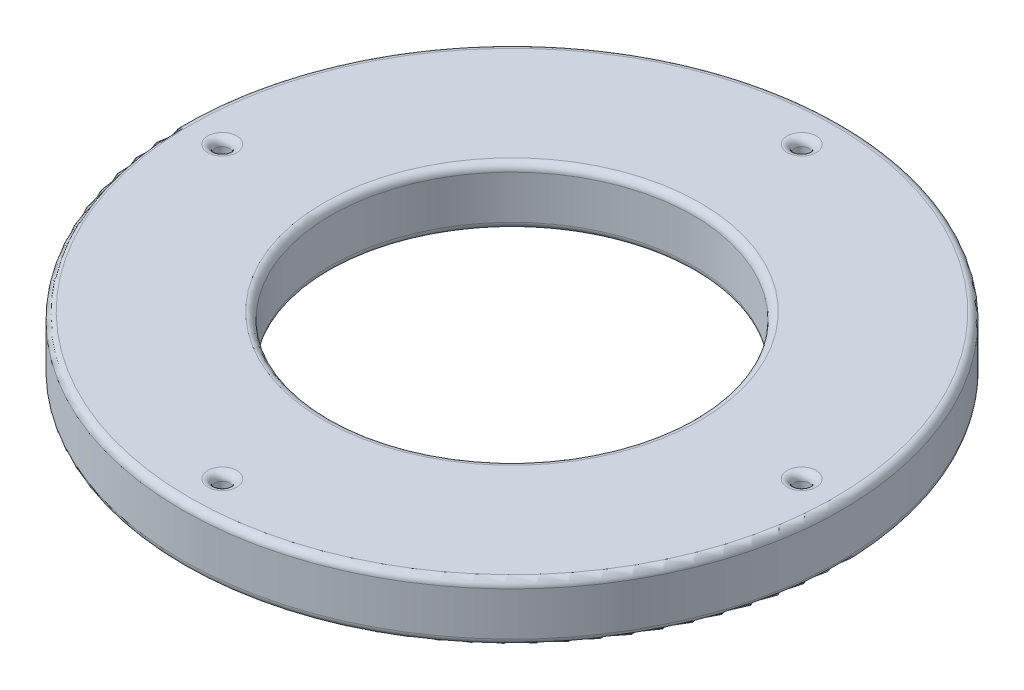
SolidWorks part; units mm, degrees
ref_plane "Plan de face" through (0, 0, 0) normal (0, 0, 1) x (1, 0, 0)
ref_plane "Plan de dessus" through (0, 0, 0) normal (0, 1, 0) x (1, 0, 0)
ref_plane "Plan de droite" through (0, 0, 0) normal (1, 0, 0) x (0, 0, -1)
sketch "Esquisse1" plane through (0, 0, 0) normal (0, 1, 0) x (1, 0, 0)
  circle A0 centre (0, 0) radius 12.5
  circle A1 centre (0, 0) radius 22.75
  circle A2 centre (20, 0) radius 0.5
  circle A3 centre (0, -20) radius 0.5
  circle A4 centre (-20, 0) radius 0.5
  circle A5 centre (0, 20) radius 0.5
  point P15 (0, 0)
  dimension "D1" = 25
  dimension "D2" = 45.5
  dimension "D3" = 1
  dimension "D4" = 20
  dimension "D5" = 4
extrude "Boss.-Extru.1" add sketch "Esquisse1" along normal blind 4
fillet "Congé1" radius 0.5 4 edges at (0, 0, 12.5) (0, 4, 12.5) (0, 0, 22.75) (0, 4, 22.75)
fillet "Congé2" radius 0.5 8 edges at (20, 0, 0.5) (20, 4, 0.5) (0, 0, -19.5) (0, 4, -19.5) (-20, 0, 0.5) (-20, 4, 0.5) (0, 0, 20.5) (0, 4, 20.5)
